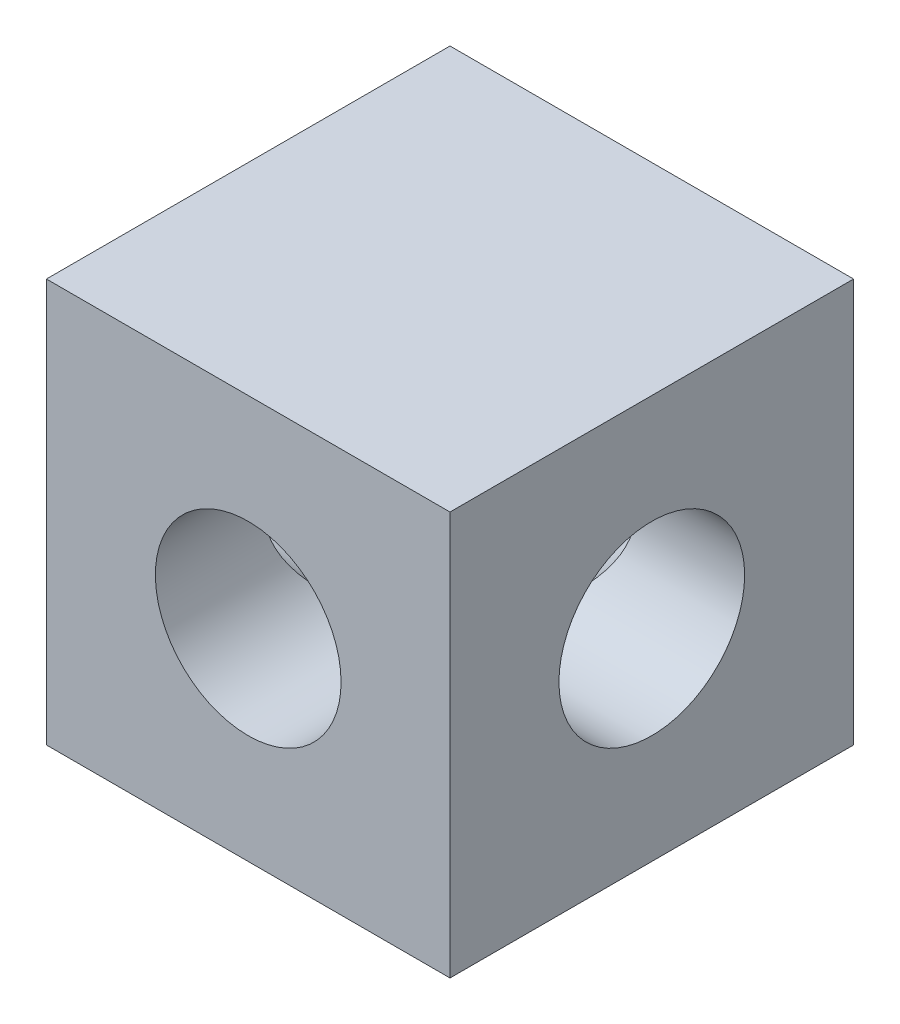
SolidWorks part; units mm, degrees
ref_plane "Front Plane" through (0, 0, 0) normal (0, 0, 1) x (1, 0, 0)
ref_plane "Top Plane" through (0, 0, 0) normal (0, 1, 0) x (1, 0, 0)
ref_plane "Right Plane" through (0, 0, 0) normal (1, 0, 0) x (0, 0, -1)
sketch "Sketch1" plane through (0, 0, 0) normal (0, 0, 1) x (1, 0, 0)
  line L0 (-26.3255, 0) -> (20.9781, 0) construction
  line L2 (-10.16, -10.16) -> (10.16, -10.16)
  line L3 (-10.16, -10.16) -> (-10.16, 10.16)
  line L4 (-10.16, 10.16) -> (10.16, 10.16)
  line L5 (10.16, -10.16) -> (10.16, 10.16)
  line L6 (-10.16, -10.16) -> (10.16, 10.16) construction
  line L7 (-10.16, 10.16) -> (10.16, -10.16) construction
  circle A0 centre (0, 0) radius 4.675
  point P3 (0, 0)
  dimension "D3" = 9.35
  dimension "D1" = 20.32
  dimension "D2" = 20.32
extrude "Boss-Extrude1" add sketch "Sketch1" along normal blind 20.32
hole_wizard "Ø20.0 (20) Diameter Hole1" positions "Sketch2" profile "Sketch3" hole size "Ø20.0" standard "ISO"
sketch "Sketch2" plane through (10.16, 0, 0) normal (1, 0, 0) x (0, 0, -1)
  line L0 (0, -10.16) -> (0, 10.16) construction
  line L2 (-20.32, 10.16) -> (0, 10.16) construction
  point P0 (-10.16, 0)
  point P9 (-9.9566, 10.16)
  dimension "D1" = 10.16
  dimension "D2" = 10.16
sketch "Sketch3" plane through (10.16, 0, 10.16) normal (0, 1, 0) x (0, 0, -1)
  line L0 (0, 0) -> (0, 23.129)
  line L1 (0, 23.129) -> (4.675, 20.32)
  line L2 (4.675, 20.32) -> (4.675, 0)
  line L5 (4.675, 0) -> (0, 0)
  line L10 (0, 23.129) -> (-4.675, 20.32) construction
  line L11 (0, -6.35) -> (0, 107.95) construction
  dimension "Hole Dia." = 9.35
  dimension "Hole Depth" = 20.32
  dimension "Drill Angle" = 118
